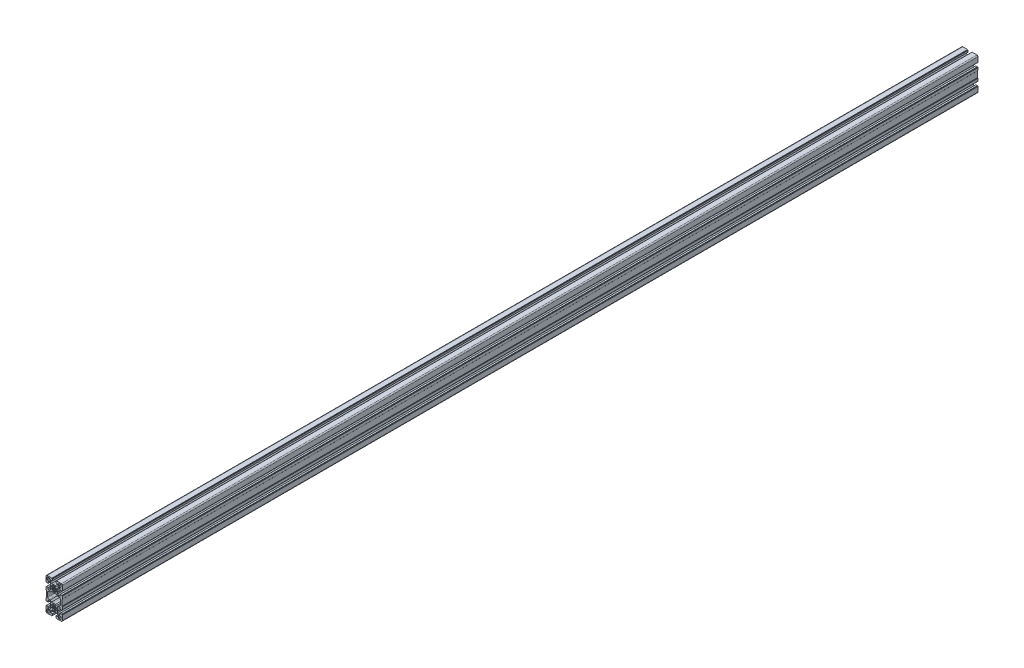
SolidWorks part; units mm, degrees
material "АД31 ГОСТ 4784-97"
ref_plane "Front Plane" through (0, 0, 0) normal (0, 0, 1) x (1, 0, 0)
ref_plane "Top Plane" through (0, 0, 0) normal (0, 1, 0) x (1, 0, 0)
ref_plane "Right Plane" through (0, 0, 0) normal (1, 0, 0) x (0, 0, -1)
sketch "Sketch1" plane through (0, 0, 0) normal (0, 0, 1) x (1, 0, 0)
  line L0 (-18.4999, 34.4999) -> (-12.9999, 34.4999)
  line L1 (-19.4999, 35.4999) -> (-19.4999, 40.9999)
  line L2 (-18.4999, 41.9999) -> (-12.9999, 41.9999)
  line L3 (-11.9999, 35.4999) -> (-11.9999, 40.9999)
  line L4 (22.4999, -16.2002) -> (22.4999, -9.2501)
  line L5 (21.9999, -8.7501) -> (20.9999, -8.7501)
  line L6 (20.9999, -8.7501) -> (20.9999, 8.7499)
  line L7 (20.9999, 8.7499) -> (21.9999, 8.7499)
  line L8 (22.4999, 9.2499) -> (22.4999, 16.1999)
  line L9 (21.9999, 16.6999) -> (20.9999, 16.6999)
  line L10 (20.9999, 16.6999) -> (20.9999, 17.5)
  line L11 (20.9999, 17.5) -> (16.5, 17.5)
  line L12 (16.5, 17.5) -> (16.5, 12.45)
  line L13 (16.5, 12.45) -> (12.3429, 12.45)
  line L14 (12.3429, 12.45) -> (9.4999, 15.293)
  line L15 (9.4999, 15.293) -> (9.4999, 19.3774)
  line L16 (9.4999, 25.6227) -> (9.4999, 29.707)
  line L17 (9.4999, 29.707) -> (12.3429, 32.55)
  line L18 (12.3429, 32.55) -> (16.5, 32.55)
  line L19 (16.5, 32.55) -> (16.5, 27.5)
  line L20 (16.5, 27.5) -> (21, 27.5)
  line L21 (21, 27.5) -> (21, 28.3)
  line L22 (21, 28.3) -> (21.9999, 28.3)
  line L23 (22.4999, 28.8) -> (22.4999, 42)
  line L24 (6.3, 45) -> (19.5, 45)
  line L25 (5.8, 44.5) -> (5.8, 43.4999)
  line L26 (5.8, 43.4999) -> (4.9999, 43.4999)
  line L27 (4.9999, 43.4999) -> (4.9999, 38.9999)
  line L28 (4.9999, 38.9999) -> (10.0499, 38.9999)
  line L29 (10.0499, 38.9999) -> (10.0499, 34.8428)
  line L30 (10.0499, 34.8428) -> (7.2069, 31.9999)
  line L31 (7.2069, 31.9999) -> (3.1226, 31.9999)
  line L32 (-3.1227, 31.9999) -> (-7.2071, 31.9999)
  line L33 (-7.2071, 31.9999) -> (-10.05, 34.8428)
  line L34 (-10.05, 34.8428) -> (-10.05, 38.9999)
  line L35 (-10.05, 38.9999) -> (-5.0001, 38.9999)
  line L36 (-5.0001, 38.9999) -> (-5.0001, 43.4999)
  line L37 (-5.0001, 43.4999) -> (-5.8001, 43.4999)
  line L38 (-5.8001, 43.4999) -> (-5.8001, 44.5)
  line L39 (-6.3001, 45) -> (-19.5001, 45)
  line L40 (-22.5001, 28.7998) -> (-22.5001, 42)
  line L41 (-22.0001, 28.2998) -> (-21, 28.2998)
  line L42 (-21, 28.2998) -> (-21, 27.5003)
  line L43 (-21, 27.5003) -> (-16.5, 27.5003)
  line L44 (-16.5, 27.5003) -> (-16.5, 32.5498)
  line L45 (-16.5, 32.5498) -> (-12.3429, 32.5498)
  line L46 (-12.3429, 32.5498) -> (-9.5, 29.7068)
  line L47 (-9.5, 29.7068) -> (-9.5, 25.6224)
  line L48 (-9.5, 19.3771) -> (-9.5, 15.2928)
  line L49 (-9.5, 15.2928) -> (-12.3429, 12.4498)
  line L50 (-12.3429, 12.4498) -> (-16.5, 12.4498)
  line L51 (-16.5, 12.4498) -> (-16.5, 17.4998)
  line L52 (-16.5, 17.4998) -> (-21, 17.4998)
  line L53 (-21, 17.4998) -> (-21, 16.6998)
  line L54 (-21, 16.6998) -> (-22.0001, 16.6998)
  line L55 (-22.5001, 9.25) -> (-22.5001, 16.1998)
  line L56 (-22.0001, 8.75) -> (-21.0001, 8.75)
  line L57 (-21.0001, 8.75) -> (-21.0001, -8.7501)
  line L58 (-21.0001, -8.7501) -> (-22.0001, -8.7501)
  line L59 (-22.5001, -16.2) -> (-22.5001, -9.2501)
  line L60 (-22.0001, -16.7) -> (-21, -16.7)
  line L61 (-21, -16.7) -> (-21, -17.5)
  line L62 (-21, -17.5) -> (-16.5, -17.5)
  line L63 (-16.5, -17.5) -> (-16.5, -12.45)
  line L64 (-16.5, -12.45) -> (-12.3429, -12.45)
  line L65 (-12.3429, -12.45) -> (-9.4999, -15.293)
  line L66 (-9.4999, -15.293) -> (-9.4999, -19.3773)
  line L67 (-9.4999, -25.6226) -> (-9.4999, -29.707)
  line L68 (-9.4999, -29.707) -> (-12.3429, -32.55)
  line L69 (-12.3429, -32.55) -> (-16.5, -32.55)
  line L70 (-16.5, -32.55) -> (-16.5, -27.4999)
  line L71 (-16.5, -27.4999) -> (-21, -27.4999)
  line L72 (-21, -27.4999) -> (-21, -28.2999)
  line L73 (-21, -28.2999) -> (-22.0001, -28.2999)
  line L74 (-22.5001, -28.7999) -> (-22.5001, -42)
  line L75 (-19.5001, -45) -> (-6.3001, -45)
  line L76 (-5.8001, -44.5) -> (-5.8001, -43.5)
  line L77 (-5.8001, -43.5) -> (-5.0002, -43.5)
  line L78 (-5.0002, -43.5) -> (-5.0002, -39)
  line L79 (-5.0002, -39) -> (-10.0501, -39)
  line L80 (-10.0501, -39) -> (-10.0501, -34.8429)
  line L81 (-10.0501, -34.8429) -> (-7.2072, -31.9999)
  line L82 (-7.2072, -31.9999) -> (-3.1228, -31.9999)
  line L83 (3.1225, -31.9999) -> (7.2069, -31.9999)
  line L84 (7.2069, -31.9999) -> (10.0498, -34.8429)
  line L85 (10.0498, -34.8429) -> (10.0498, -39)
  line L86 (10.0498, -39) -> (5, -39)
  line L87 (5, -39) -> (5, -43.5)
  line L88 (5, -43.5) -> (5.7999, -43.5)
  line L89 (5.7999, -43.5) -> (5.7999, -44.5)
  line L90 (6.2999, -45) -> (19.5, -45)
  line L91 (22.4999, -42) -> (22.4999, -28.8002)
  line L92 (21.9999, -28.3002) -> (20.9999, -28.3002)
  line L93 (20.9999, -28.3002) -> (20.9999, -27.5001)
  line L94 (20.9999, -27.5001) -> (16.5001, -27.5001)
  line L95 (16.5001, -27.5001) -> (16.5001, -32.5501)
  line L96 (16.5001, -32.5501) -> (12.343, -32.5501)
  line L97 (12.343, -32.5501) -> (9.5, -29.7072)
  line L98 (9.5, -29.7072) -> (9.5, -25.6228)
  line L99 (9.5, -19.3775) -> (9.5, -15.2931)
  line L100 (9.5, -15.2931) -> (12.343, -12.4502)
  line L101 (12.343, -12.4502) -> (16.5001, -12.4502)
  line L102 (16.5001, -12.4502) -> (16.5001, -17.4998)
  line L103 (16.5001, -17.4998) -> (21, -17.4998)
  line L104 (21, -17.4998) -> (21, -16.7002)
  line L105 (21, -16.7002) -> (21.9999, -16.7002)
  line L106 (2.8679, -26.5958) -> (4.5886, -29.0533)
  line L107 (1.3892, -30.3785) -> (0.8683, -27.4241)
  line L108 (-1.3892, -30.3785) -> (-0.8682, -27.4241)
  line L109 (-4.5886, -29.0533) -> (-2.8679, -26.5958)
  line L110 (-6.5532, -27.0887) -> (-4.0957, -25.368)
  line L111 (-7.8784, -23.8893) -> (-4.924, -23.3683)
  line L112 (-4.924, -21.6318) -> (-7.8784, -21.1109)
  line L113 (-6.5532, -17.9115) -> (-4.0957, -19.6322)
  line L114 (-2.8679, -18.4043) -> (-4.5886, -15.9469)
  line L115 (-1.3892, -14.6216) -> (-0.8682, -17.5761)
  line L116 (0.8683, -17.5761) -> (1.3892, -14.6216)
  line L117 (2.8679, -18.4043) -> (4.5886, -15.9469)
  line L118 (4.0958, -19.6322) -> (6.5532, -17.9115)
  line L119 (4.924, -21.6318) -> (7.8784, -21.1109)
  line L120 (4.924, -23.3683) -> (7.8784, -23.8893)
  line L121 (6.5532, -27.0887) -> (4.0957, -25.368)
  line L122 (-18.4999, -34.5001) -> (-12.9999, -34.5001)
  line L123 (-19.4999, -41) -> (-19.4999, -35.5001)
  line L124 (-18.4999, -42) -> (-12.9999, -42)
  line L125 (-11.9999, -41) -> (-11.9999, -35.5001)
  line L126 (13, -34.5001) -> (18.5, -34.5001)
  line L127 (19.5, -41) -> (19.5, -35.5001)
  line L128 (13, -42) -> (18.5, -42)
  line L129 (12, -41) -> (12, -35.5001)
  line L130 (2.8679, 26.5957) -> (4.5886, 29.0531)
  line L131 (0.8683, 27.424) -> (1.3892, 30.3784)
  line L132 (-0.8682, 27.424) -> (-1.3892, 30.3784)
  line L133 (-4.5886, 29.0532) -> (-2.8679, 26.5957)
  line L134 (-4.0957, 25.3678) -> (-6.5532, 27.0886)
  line L135 (-7.8784, 23.8891) -> (-4.924, 23.3682)
  line L136 (-7.8784, 21.1108) -> (-4.924, 21.6317)
  line L137 (-6.5532, 17.9113) -> (-4.0958, 19.6321)
  line L138 (-4.5886, 15.9467) -> (-2.8679, 18.4042)
  line L139 (-1.3892, 14.6215) -> (-0.8682, 17.5759)
  line L140 (0.8683, 17.5759) -> (1.3892, 14.6215)
  line L141 (4.5886, 15.9467) -> (2.8679, 18.4042)
  line L142 (4.0958, 19.6321) -> (6.5532, 17.9113)
  line L143 (7.8785, 21.1108) -> (4.924, 21.6317)
  line L144 (4.924, 23.3682) -> (7.8785, 23.8891)
  line L145 (4.0958, 25.3678) -> (6.5532, 27.0885)
  line L146 (-3.1224, -12.9999) -> (-7.5074, -12.9999)
  line L147 (-7.5074, -12.9999) -> (-11.0573, -9.45)
  line L148 (-11.0573, -9.45) -> (-14, -9.45)
  line L149 (-18, -5.45) -> (-18, 5.45)
  line L150 (-14, 9.45) -> (-11.0573, 9.45)
  line L151 (-11.0573, 9.45) -> (-7.5074, 12.9999)
  line L152 (-7.5074, 12.9999) -> (-3.1224, 12.9999)
  line L153 (3.1226, 13) -> (7.5074, 13)
  line L154 (7.5074, 13) -> (11.0574, 9.45)
  line L155 (11.0574, 9.45) -> (14, 9.45)
  line L156 (18, -5.45) -> (18, 5.4499)
  line L157 (14, -9.45) -> (11.0574, -9.45)
  line L158 (11.0574, -9.45) -> (7.5074, -13)
  line L159 (7.5074, -13) -> (3.1226, -13)
  line L160 (12, 40.9999) -> (12, 35.4999)
  line L161 (13, 34.4999) -> (18.5, 34.4999)
  line L162 (19.5, 35.4999) -> (19.5, 40.9999)
  line L163 (18.5, 41.9999) -> (13, 41.9999)
  line L164 (-23.6439, 0) -> (25.0938, 0) construction
  line L165 (-0.0001, -50.4543) -> (-0.0001, 46.779) construction
  line L166 (-27.422, -22.5) -> (30.9458, -22.5) construction
  line L167 (-27.422, 22.5) -> (28.7661, 22.5) construction
  arc A0 (18.5, 34.4999) -> (19.5, 35.4999) centre (18.5, 35.4999) ccw
  arc A1 (19.5, 40.9999) -> (18.5, 41.9999) centre (18.5, 40.9999) ccw
  arc A2 (13, 41.9999) -> (12, 40.9999) centre (13, 40.9999) ccw
  arc A3 (12, 35.4999) -> (13, 34.4999) centre (13, 35.4999) ccw
  arc A4 (-19.4999, 35.4999) -> (-18.4999, 34.4999) centre (-18.4999, 35.4999) ccw
  arc A5 (-18.4999, 41.9999) -> (-19.4999, 40.9999) centre (-18.4999, 40.9999) ccw
  arc A6 (-11.9999, 40.9999) -> (-12.9999, 41.9999) centre (-12.9999, 40.9999) ccw
  arc A7 (-12.9999, 34.4999) -> (-11.9999, 35.4999) centre (-12.9999, 35.4999) ccw
  arc A8 (21.9999, -16.7002) -> (22.4999, -16.2002) centre (21.9999, -16.2002) ccw
  arc A9 (22.4999, -9.2501) -> (21.9999, -8.7501) centre (21.9999, -9.2501) ccw
  arc A10 (21.9999, 8.7499) -> (22.4999, 9.2499) centre (21.9999, 9.2499) ccw
  arc A11 (22.4999, 16.1999) -> (21.9999, 16.6999) centre (21.9999, 16.1999) ccw
  arc A12 (9.4999, 19.3774) -> (9.4999, 25.6227) centre (0, 22.5) ccw
  arc A13 (21.9999, 28.3) -> (22.4999, 28.8) centre (21.9999, 28.8) ccw
  arc A14 (22.4999, 42) -> (19.5, 45) centre (19.5, 42) ccw
  arc A15 (6.3, 45) -> (5.8, 44.5) centre (6.3, 44.5) ccw
  arc A16 (3.1226, 31.9999) -> (-3.1227, 31.9999) centre (-0.0001, 22.5) ccw
  arc A17 (-5.8001, 44.5) -> (-6.3001, 45) centre (-6.3001, 44.5) ccw
  arc A18 (-19.5001, 45) -> (-22.5001, 42) centre (-19.5001, 42) ccw
  arc A19 (-22.5001, 28.7998) -> (-22.0001, 28.2998) centre (-22.0001, 28.7998) ccw
  arc A20 (-9.5, 25.6224) -> (-9.5, 19.3771) centre (-0.0001, 22.4998) ccw
  arc A21 (-22.0001, 16.6998) -> (-22.5001, 16.1998) centre (-22.0001, 16.1998) ccw
  arc A22 (-22.5001, 9.25) -> (-22.0001, 8.75) centre (-22.0001, 9.25) ccw
  arc A23 (-22.0001, -8.7501) -> (-22.5001, -9.2501) centre (-22.0001, -9.2501) ccw
  arc A24 (-22.5001, -16.2) -> (-22.0001, -16.7) centre (-22.0001, -16.2) ccw
  arc A25 (-9.4999, -19.3773) -> (-9.4999, -25.6226) centre (0, -22.5) ccw
  arc A26 (-22.0001, -28.2999) -> (-22.5001, -28.7999) centre (-22.0001, -28.7999) ccw
  arc A27 (-22.5001, -42) -> (-19.5001, -45) centre (-19.5001, -42) ccw
  arc A28 (-6.3001, -45) -> (-5.8001, -44.5) centre (-6.3001, -44.5) ccw
  arc A29 (-3.1228, -31.9999) -> (3.1225, -31.9999) centre (-0.0001, -22.5) ccw
  arc A30 (5.7999, -44.5) -> (6.2999, -45) centre (6.2999, -44.5) ccw
  arc A31 (19.5, -45) -> (22.4999, -42) centre (19.5, -42) ccw
  arc A32 (22.4999, -28.8002) -> (21.9999, -28.3002) centre (21.9999, -28.8002) ccw
  arc A33 (9.5, -25.6228) -> (9.5, -19.3775) centre (0.0001, -22.5001) ccw
  arc A34 (1.3892, -30.3785) -> (4.5886, -29.0533) centre (0, -22.5001) ccw
  arc A35 (-0.8682, -27.4241) -> (0.8683, -27.4241) centre (0, -22.5001) ccw
  arc A36 (-4.5886, -29.0533) -> (-1.3892, -30.3785) centre (0, -22.5001) ccw
  arc A37 (-4.0957, -25.368) -> (-2.8679, -26.5958) centre (0, -22.5001) ccw
  arc A38 (-7.8784, -23.8893) -> (-6.5532, -27.0887) centre (0, -22.5001) ccw
  arc A39 (-4.924, -21.6318) -> (-4.924, -23.3683) centre (0, -22.5001) ccw
  arc A40 (-6.5532, -17.9115) -> (-7.8784, -21.1109) centre (0, -22.5001) ccw
  arc A41 (-2.8679, -18.4043) -> (-4.0957, -19.6322) centre (0, -22.5001) ccw
  arc A42 (-1.3892, -14.6216) -> (-4.5886, -15.9469) centre (0, -22.5001) ccw
  arc A43 (0.8683, -17.5761) -> (-0.8682, -17.5761) centre (0, -22.5001) ccw
  arc A44 (4.5886, -15.9469) -> (1.3892, -14.6216) centre (0, -22.5001) ccw
  arc A45 (4.0958, -19.6322) -> (2.8679, -18.4043) centre (0, -22.5001) ccw
  arc A46 (7.8784, -21.1109) -> (6.5532, -17.9115) centre (0, -22.5001) ccw
  arc A47 (4.924, -23.3683) -> (4.924, -21.6318) centre (0, -22.5001) ccw
  arc A48 (6.5532, -27.0887) -> (7.8784, -23.8893) centre (0, -22.5001) ccw
  arc A49 (2.8679, -26.5958) -> (4.0957, -25.368) centre (0, -22.5001) ccw
  arc A50 (-18.4999, -34.5001) -> (-19.4999, -35.5001) centre (-18.4999, -35.5001) ccw
  arc A51 (-19.4999, -41) -> (-18.4999, -42) centre (-18.4999, -41) ccw
  arc A52 (-12.9999, -42) -> (-11.9999, -41) centre (-12.9999, -41) ccw
  arc A53 (-11.9999, -35.5001) -> (-12.9999, -34.5001) centre (-12.9999, -35.5001) ccw
  arc A54 (19.5, -35.5001) -> (18.5, -34.5001) centre (18.5, -35.5001) ccw
  arc A55 (18.5, -42) -> (19.5, -41) centre (18.5, -41) ccw
  arc A56 (12, -41) -> (13, -42) centre (13, -41) ccw
  arc A57 (13, -34.5001) -> (12, -35.5001) centre (13, -35.5001) ccw
  arc A58 (4.5886, 29.0531) -> (1.3892, 30.3784) centre (0, 22.5) ccw
  arc A59 (0.8683, 27.424) -> (-0.8682, 27.424) centre (0, 22.4999) ccw
  arc A60 (-1.3892, 30.3784) -> (-4.5886, 29.0532) centre (0, 22.5) ccw
  arc A61 (-2.8679, 26.5957) -> (-4.0957, 25.3678) centre (0, 22.4999) ccw
  arc A62 (-6.5532, 27.0886) -> (-7.8784, 23.8891) centre (0, 22.5) ccw
  arc A63 (-4.924, 23.3682) -> (-4.924, 21.6317) centre (0, 22.4999) ccw
  arc A64 (-7.8784, 21.1108) -> (-6.5532, 17.9113) centre (0, 22.4999) ccw
  arc A65 (-4.0958, 19.6321) -> (-2.8679, 18.4042) centre (0, 22.4999) ccw
  arc A66 (-4.5886, 15.9467) -> (-1.3892, 14.6215) centre (0, 22.4999) ccw
  arc A67 (-0.8682, 17.5759) -> (0.8683, 17.5759) centre (0, 22.4999) ccw
  arc A68 (1.3892, 14.6215) -> (4.5886, 15.9467) centre (0, 22.4999) ccw
  arc A69 (2.8679, 18.4042) -> (4.0958, 19.6321) centre (0, 22.4999) ccw
  arc A70 (6.5532, 17.9113) -> (7.8785, 21.1108) centre (0, 22.4999) ccw
  arc A71 (4.924, 21.6317) -> (4.924, 23.3682) centre (0, 22.4999) ccw
  arc A72 (7.8785, 23.8891) -> (6.5532, 27.0885) centre (0, 22.4999) ccw
  arc A73 (4.0958, 25.3678) -> (2.8679, 26.5957) centre (0, 22.4999) ccw
  arc A74 (3.1226, -13) -> (-3.1224, -12.9999) centre (0, -22.4999) ccw
  arc A75 (-18, -5.45) -> (-14, -9.45) centre (-14, -5.45) ccw
  arc A76 (-14, 9.45) -> (-18, 5.45) centre (-14, 5.45) ccw
  arc A77 (-3.1224, 12.9999) -> (3.1226, 13) centre (0, 22.5) ccw
  arc A78 (18, 5.4499) -> (14, 9.45) centre (14, 5.45) ccw
  arc A79 (14, -9.45) -> (18, -5.45) centre (14, -5.45) ccw
  dimension "D7" = 12.5
  dimension "D8" = 10
  dimension "D1" = 45
  dimension "D2" = 10
  dimension "D3" = 45
  dimension "D4" = 90
  dimension "D5" = 22.5
  dimension "D6" = 22.5
extrude "Base-Extrude" add sketch "Sketch1" against normal blind 2525
sketch "Эскиз1" plane through (0, 0, 0) normal (0, 0, 1) x (1, 0, 0)
  line L0 (-21, 27.5003) -> (-21, 17.4998)
  line L1 (-21, 22.5) -> (-22.5001, 22.5)
  line L2 (-22.5001, 28.7998) -> (-22.5001, 16.1998)
  line L3 (-0.0001, 32.4999) -> (-0.0001, 22.5) construction
  line L4 (22.4999, 28.7998) -> (22.4999, 16.1998)
  line L5 (20.9999, 22.5) -> (22.4999, 22.5)
  line L6 (20.9999, 27.5003) -> (20.9999, 17.4998)
  line L7 (0, 0) -> (36.0278, 0) construction
  line L8 (-21, 27.5003) -> (-21, 17.4998)
  line L9 (-21, 22.5) -> (-22.5001, 22.5)
  line L10 (-22.5001, 28.7998) -> (-22.5001, 16.1998)
  line L11 (22.4999, 28.7998) -> (22.4999, 16.1998)
  line L12 (20.9999, 22.5) -> (22.4999, 22.5)
  line L13 (20.9999, 27.5003) -> (20.9999, 17.4998)
  line L14 (-21, 27.5003) -> (-21, 17.4998)
  line L15 (-21, 22.5) -> (-22.5001, 22.5)
  line L16 (-22.5001, 28.7998) -> (-22.5001, 16.1998)
  line L17 (22.4999, 28.7998) -> (22.4999, 16.1998)
  line L18 (20.9999, 22.5) -> (22.4999, 22.5)
  line L19 (20.9999, 27.5003) -> (20.9999, 17.4998)
  line L20 (-21, 27.5003) -> (-21, 17.4998)
  line L21 (-21, 22.5) -> (-22.5001, 22.5)
  line L22 (-22.5001, 28.7998) -> (-22.5001, 16.1998)
  line L23 (22.4999, 28.7998) -> (22.4999, 16.1998)
  line L24 (20.9999, 22.5) -> (22.4999, 22.5)
  line L25 (20.9999, 27.5003) -> (20.9999, 17.4998)
  line L26 (20.9999, -27.5003) -> (20.9999, -17.4998)
  line L27 (20.9999, -22.5) -> (22.4999, -22.5)
  line L28 (22.4999, -28.7998) -> (22.4999, -16.1998)
  line L29 (-22.5001, -28.7998) -> (-22.5001, -16.1998)
  line L30 (-21, -22.5) -> (-22.5001, -22.5)
  line L31 (-21, -27.5003) -> (-21, -17.4998)
  line L32 (20.9999, -27.5003) -> (20.9999, -17.4998)
  line L33 (20.9999, -22.5) -> (22.4999, -22.5)
  line L34 (22.4999, -28.7998) -> (22.4999, -16.1998)
  line L35 (-22.5001, -28.7998) -> (-22.5001, -16.1998)
  line L36 (-21, -22.5) -> (-22.5001, -22.5)
  line L37 (-21, -27.5003) -> (-21, -17.4998)
  line L38 (20.9999, -27.5003) -> (20.9999, -17.4998)
  line L39 (20.9999, -22.5) -> (22.4999, -22.5)
  line L40 (22.4999, -28.7998) -> (22.4999, -16.1998)
  line L41 (-22.5001, -28.7998) -> (-22.5001, -16.1998)
  line L42 (-21, -22.5) -> (-22.5001, -22.5)
  line L43 (-21, -27.5003) -> (-21, -17.4998)
  line L44 (20.9999, -27.5003) -> (20.9999, -17.4998)
  line L45 (20.9999, -22.5) -> (22.4999, -22.5)
  line L46 (22.4999, -28.7998) -> (22.4999, -16.1998)
  line L47 (-22.5001, -28.7998) -> (-22.5001, -16.1998)
  line L48 (-21, -22.5) -> (-22.5001, -22.5)
  line L49 (-21, -27.5003) -> (-21, -17.4998)
  arc A0 (3.1226, 31.9999) -> (-3.1227, 31.9999) centre (-0.0001, 22.5) ccw construction
